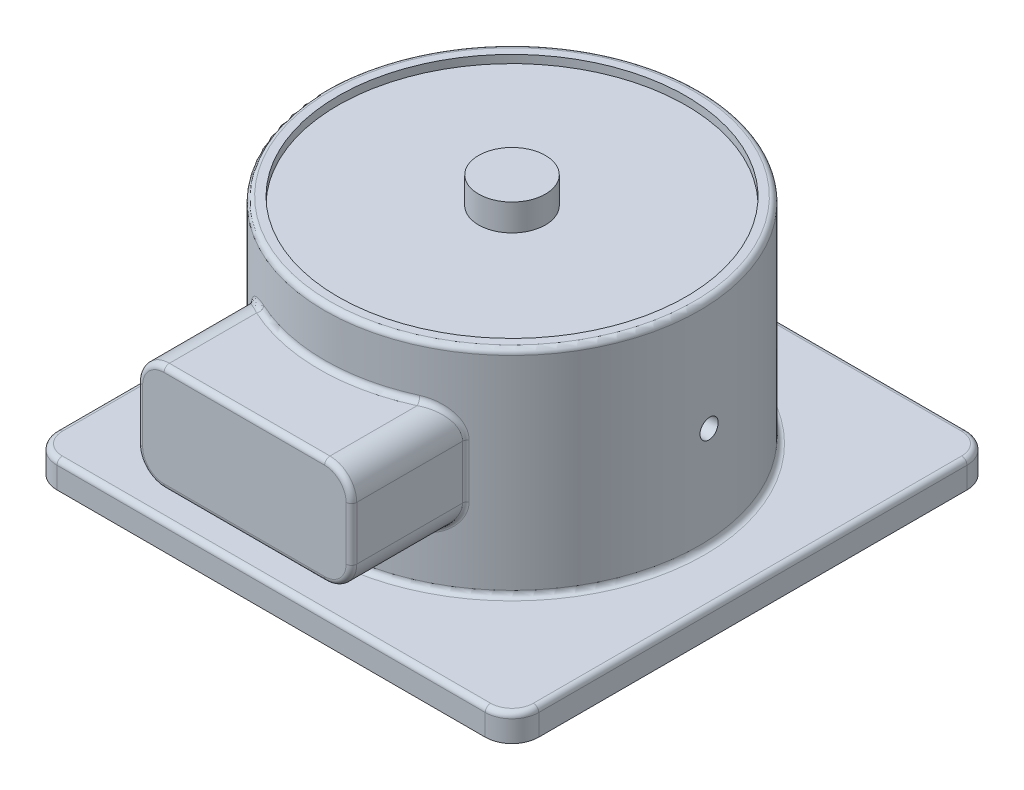
SolidWorks part; units mm, degrees
ref_plane "Front Plane" through (0, 0, 0) normal (0, 0, 1) x (1, 0, 0)
ref_plane "Top Plane" through (0, 0, 0) normal (0, 1, 0) x (1, 0, 0)
ref_plane "Right Plane" through (0, 0, 0) normal (1, 0, 0) x (0, 0, -1)
sketch "Sketch1" plane through (0, 0, 0) normal (0, 1, 0) x (1, 0, 0)
  line L1 (-90, 90) -> (90, 90)
  line L2 (-90, 90) -> (-90, -90)
  line L3 (-90, -90) -> (90, -90)
  line L4 (90, 90) -> (90, -90)
  line L5 (-90, 90) -> (90, -90) construction
  line L6 (-90, -90) -> (90, 90) construction
  point P0 (0, 0)
  dimension "D1" = 180
extrude "Boss-Extrude1" add sketch "Sketch1" along normal blind 10
sketch "Sketch2" plane through (0, 10, 0) normal (0, 1, 0) x (1, 0, 0)
  circle A0 centre (0, 0) radius 70
  dimension "D1" = 140
extrude "Boss-Extrude2" add sketch "Sketch2" along normal blind 80
sketch "Sketch3" plane through (0, 0, 0) normal (0, 0, 1) x (1, 0, 0)
  line L1 (40, 30) -> (-40, 30)
  line L2 (40, 30) -> (40, 70)
  line L3 (40, 70) -> (-40, 70)
  line L4 (-40, 30) -> (-40, 70)
  line L5 (40, 30) -> (-40, 70) construction
  line L6 (40, 70) -> (-40, 30) construction
  point P0 (0, 50)
  dimension "D1" = 40
  dimension "D2" = 80
  dimension "D3" = 50
extrude "Boss-Extrude3" add sketch "Sketch3" along normal blind 100
sketch3d "3DSketch1"
  spline S0 degree 3 poles (-9.0372, 90, 64.5805) (0.0853, 90, 65.2157) (9.2936, 90, 64.5563) (18.3975, 90, 62.5733) (27.126, 90, 59.3133) (35.3009, 90, 54.8428) (42.7554, 90, 49.2531) (49.3373, 90, 42.6582) (54.9123, 90, 35.1927) (59.3667, 90, 27.009) (62.6095, 90, 18.2741) (64.5745, 90, 9.1663) (65.2217, 90, -0.1286) (64.5379, 90, -9.4209) (62.5369, 90, -18.5209) (59.2597, 90, -27.2429) (54.7731, 90, -35.409) (49.1687, 90, -42.8524) (42.5608, 90, -49.4213) (35.0844, 90, -54.9816) (26.8919, 90, -59.4198) (18.1507, 90, -62.6454) (9.039, 90, -64.5925) (-0.2572, 90, -65.2213) (-9.5481, 90, -64.5192) (-18.6441, 90, -62.5003) (-27.3597, 90, -59.2059) (-35.5169, 90, -54.7032) (-42.9493, 90, -49.0841) (-49.5051, 90, -42.4633) (-55.0506, 90, -34.9759) (-59.4727, 90, -26.7747) (-62.681, 90, -18.0271) (-64.6102, 90, -8.9116) (-65.2207, 90, 0.3858) (-64.5002, 90, 9.6753) (-62.4634, 90, 18.7673) (-59.1518, 90, 27.4764) (-54.6331, 90, 35.6247) (-48.9993, 90, 43.0459) (-42.3656, 90, 49.5887) (-34.8673, 90, 55.1195) (-26.6575, 90, 59.5254) (-17.9836, 90, 62.6872) (-9.0372, 90, 64.5805) (0.0853, 90, 65.2157) (9.2936, 90, 64.5563) knots -0.067014 -0.044258 -0.022128 0 0.022756 0.045512 0.068267 0.091023 0.113779 0.136535 0.15929 0.182046 0.204802 0.227558 0.250313 0.273069 0.295825 0.318581 0.341336 0.364092 0.386848 0.409604 0.432359 0.455115 0.477871 0.500627 0.523382 0.546138 0.568894 0.59165 0.614405 0.637161 0.659917 0.682673 0.705428 0.728184 0.75094 0.773696 0.796451 0.819207 0.841963 0.864719 0.887474 0.91023 0.932986 0.955742 0.977872 1 1.022756 1.045512 1.068267 only from (0, 90, 65) to (0, 90, 65)
  spline S1 degree 3 poles (-9.0372, 90, 64.5805) (0.0853, 90, 65.2157) (9.2936, 90, 64.5563) (18.3975, 90, 62.5733) (27.126, 90, 59.3133) (35.3009, 90, 54.8428) (42.7554, 90, 49.2531) (49.3373, 90, 42.6582) (54.9123, 90, 35.1927) (59.3667, 90, 27.009) (62.6095, 90, 18.2741) (64.5745, 90, 9.1663) (65.2217, 90, -0.1286) (64.5379, 90, -9.4209) (62.5369, 90, -18.5209) (59.2597, 90, -27.2429) (54.7731, 90, -35.409) (49.1687, 90, -42.8524) (42.5608, 90, -49.4213) (35.0844, 90, -54.9816) (26.8919, 90, -59.4198) (18.1507, 90, -62.6454) (9.039, 90, -64.5925) (-0.2572, 90, -65.2213) (-9.5481, 90, -64.5192) (-18.6441, 90, -62.5003) (-27.3597, 90, -59.2059) (-35.5169, 90, -54.7032) (-42.9493, 90, -49.0841) (-49.5051, 90, -42.4633) (-55.0506, 90, -34.9759) (-59.4727, 90, -26.7747) (-62.681, 90, -18.0271) (-64.6102, 90, -8.9116) (-65.2207, 90, 0.3858) (-64.5002, 90, 9.6753) (-62.4634, 90, 18.7673) (-59.1518, 90, 27.4764) (-54.6331, 90, 35.6247) (-48.9993, 90, 43.0459) (-42.3656, 90, 49.5887) (-34.8673, 90, 55.1195) (-26.6575, 90, 59.5254) (-17.9836, 90, 62.6872) (-9.0372, 90, 64.5805) (0.0853, 90, 65.2157) (9.2936, 90, 64.5563) knots -0.067014 -0.044258 -0.022128 0 0.022756 0.045512 0.068267 0.091023 0.113779 0.136535 0.15929 0.182046 0.204802 0.227558 0.250313 0.273069 0.295825 0.318581 0.341336 0.364092 0.386848 0.409604 0.432359 0.455115 0.477871 0.500627 0.523382 0.546138 0.568894 0.59165 0.614405 0.637161 0.659917 0.682673 0.705428 0.728184 0.75094 0.773696 0.796451 0.819207 0.841963 0.864719 0.887474 0.91023 0.932986 0.955742 0.977872 1 1.022756 1.045512 1.068267 only from (0, 90, 65) to (0, 90, 65)
  dimension "D1" = 5
extrude "Cut-Extrude1" cut sketch "3DSketch1" along direction (0, 1, 0) on the side of the normal blind 3
fillet "Fillet1" radius 10 8 edges at (90, 5, 90) (90, 5, -90) (-90, 5, -90) (-90, 5, 90) (-40, 30, 78.7228) (40, 30, 78.7228) (40, 70, 78.7228) (-40, 70, 78.7228)
fillet "Fillet2" radius 2 26 edges at (-87.0711, 10, 87.0711) (-90, 10, 0) (-87.0711, 10, -87.0711) (0, 10, -90) (87.0711, 10, -87.0711) (90, 10, 0) (87.0711, 10, 87.0711) (0, 10, 90) (-36.8398, 32.705, 59.5217) (0, 30, 70) (38.3695, 34.5271, 58.5473) (40, 50, 57.4456) (36.8398, 67.295, 59.5217) (0, 70, 70) (-38.3695, 65.4729, 58.5473) (-40, 50, 57.4456) (0, 90, 70) (0, 10, 70) (-37.0711, 67.0711, 100) (0, 70, 100) (37.0711, 67.0711, 100) (40, 50, 100) (37.0711, 32.9289, 100) (0, 30, 100) (-37.0711, 32.9289, 100) (-40, 50, 100)
hole_wizard "1/16 NPT Tapped Hole1" positions "3DSketch2" profile "Sketch6" size "1/16" standard "ANSI Inch"
sketch3d "3DSketch2"
  point P0 (69.8946, 47.911, -3.8402)
sketch "Sketch6" plane through (69.8946, 47.911, -3.8402) normal (0, 1, 0) x (-0.0549, 0, -0.9985)
  line L0 (0, 0) -> (0, 6.9467)
  line L1 (3.0734, 5.1) -> (0, 6.9467)
  line L2 (-3.0734, 5.1) -> (0, 6.9467) construction
  line L3 (3.0734, 5.1) -> (3.0734, 8)
  line L4 (3.0734, 8) -> (3.3648, 8)
  line L5 (3.3648, 8) -> (3.6043, 0)
  line L6 (-3.3648, 8) -> (-3.6043, 0) construction
  line L7 (3.6043, 0) -> (0, 0)
  line L8 (0, -6.35) -> (0, 107.95) construction
  line L11 (-3.0734, 8) -> (-3.3648, 8) construction
  dimension "Tap Drill Dia." = 6.1468
  dimension "Tap Drill Depth" = 5.1
  dimension "Thread Dia." = 7.2087
  dimension "Thread Angle" = 3.43
  dimension "Thread Depth" = 8
  dimension "Drill Angle" = 118
cosmetic thread "Hole Thread1" parameters "D1"=8, "D2"=8.0038
sketch "Sketch7" plane through (0, 87, 0) normal (0, 1, 0) x (1, 0, 0)
  circle A0 centre (0, 0) radius 12.5
  dimension "D1" = 25
extrude "Boss-Extrude4" add sketch "Sketch7" along normal blind 10
